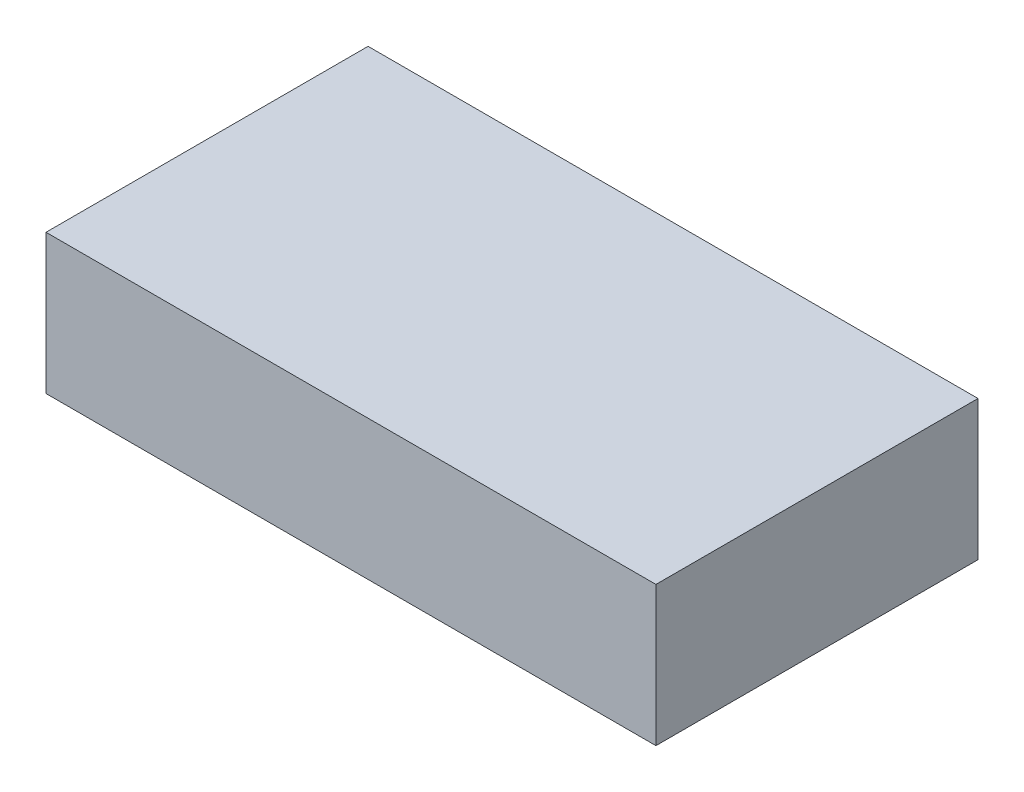
SolidWorks part; units mm, degrees
material "1060 Alloy"
ref_plane "Front" through (0, 0, 0) normal (0, 0, 1) x (1, 0, 0)
ref_plane "Top" through (0, 0, 0) normal (0, 1, 0) x (1, 0, 0)
ref_plane "Right" through (0, 0, 0) normal (1, 0, 0) x (0, 0, -1)
sketch "Sketch2" plane through (0, 0, 0) normal (0, 1, 0) x (1, 0, 0)
  line L1 (0, 0) -> (214, 0)
  line L2 (0, 0) -> (0, 113)
  line L3 (0, 113) -> (214, 113)
  line L4 (214, 0) -> (214, 113)
  dimension "D1" = 214
  dimension "D2" = 113
extrude "Boss-Extrude1" add sketch "Sketch2" along normal blind 49
